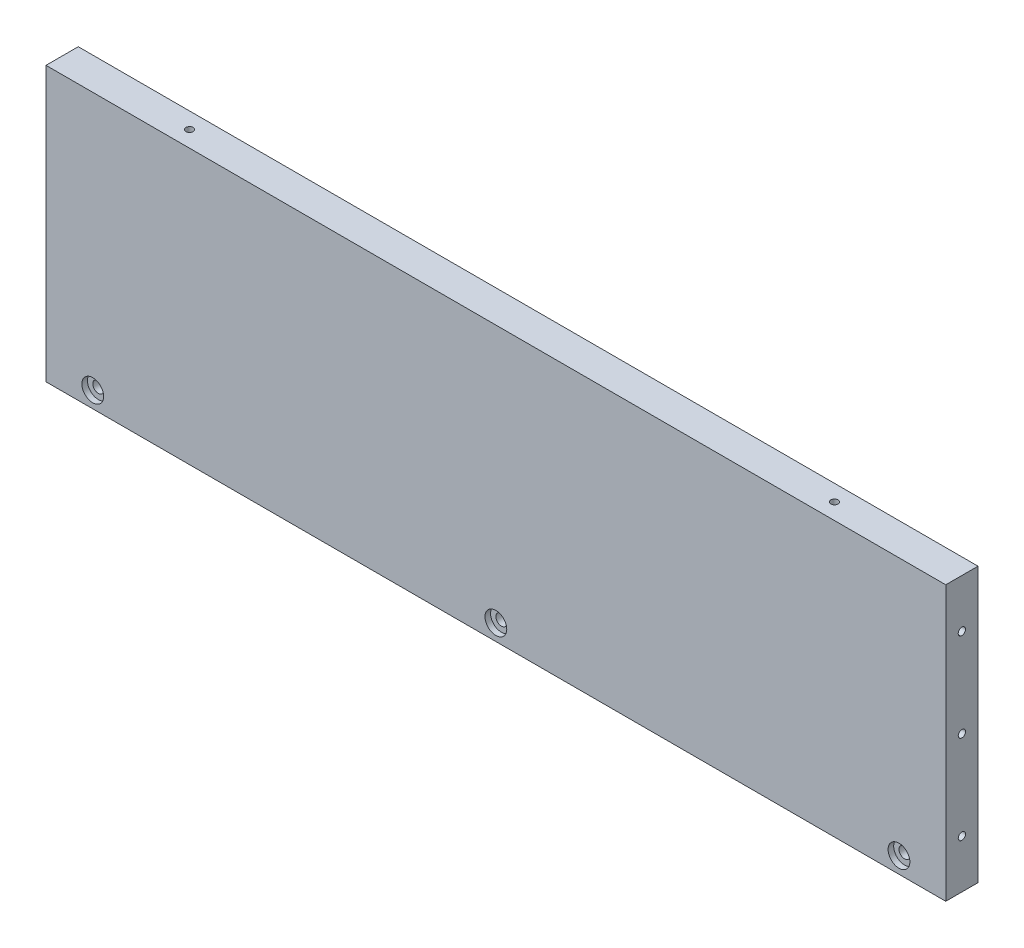
SolidWorks part; units mm, degrees
ref_plane "Front Plane" through (0, 0, 0) normal (0, 0, 1) x (1, 0, 0)
ref_plane "Top Plane" through (0, 0, 0) normal (0, 1, 0) x (1, 0, 0)
ref_plane "Right Plane" through (0, 0, 0) normal (1, 0, 0) x (0, 0, -1)
sketch "Sketch1" plane through (0, 0, 0) normal (0, 0, 1) x (1, 0, 0)
  line L1 (-130.9962, 78.0328) -> (148.0038, 78.0328)
  line L2 (-130.9962, 78.0328) -> (-130.9962, -6.9672)
  line L3 (-130.9962, -6.9672) -> (148.0038, -6.9672)
  line L4 (148.0038, 78.0328) -> (148.0038, -6.9672)
  dimension "D1" = 279
  dimension "D2" = 85
extrude "Boss-Extrude1" add sketch "Sketch1" along normal blind 10
sketch "Sketch2" plane through (0, 0, 10) normal (0, 0, 1) x (1, 0, 0)
  line L0 (-116.4962, -1.9672) -> (133.5038, -1.9672)
  line L1 (-130.9962, -6.9672) -> (148.0038, -6.9672) construction
  point P3 (8.5038, -1.9672)
  point P5 (8.5038, -6.9672)
  dimension "D1" = 5
  dimension "D2" = 250
  dimension "D3" = 0
hole_wizard "CBORE for #4 Binding Head Machine Screw1" positions "Sketch5" profile "Sketch4" counterbore size "#4" standard "ANSI Inch" end condition through all
sketch "Sketch5" plane through (0, 0, 10) normal (0, 0, 1) x (1, 0, 0)
  point P0 (-116.4962, -1.9672)
  point P3 (8.5038, -1.9672)
  point P6 (133.5038, -1.9672)
sketch "Sketch4" plane through (-116.4962, -1.9672, 10) normal (1, 0, 0) x (0, -1, 0)
  line L0 (0, 0) -> (0, 10)
  line L1 (0, 10) -> (1.7272, 10)
  line L3 (1.7272, 10) -> (1.7272, 1.7272)
  line L4 (1.7272, 1.7272) -> (3.3731, 1.7272)
  line L5 (3.3731, 1.7272) -> (3.3731, 0)
  line L7 (3.3731, 0) -> (0, 0)
  line L11 (0, -6.35) -> (0, 107.95) construction
  dimension "Thru Hole Dia." = 3.4544
  dimension "Thru Hole Depth" = 10
  dimension "C'Bore Dia." = 6.7462
  dimension "C'Bore Depth" = 1.7272
sketch "Sketch6" plane through (-130.9962, 0, 0) normal (-1, 0, 0) x (0, 0, 1)
  line L0 (0, 35.5328) -> (10, 35.5328)
  line L1 (0, 78.0328) -> (0, -6.9672) construction
  line L2 (10, 78.0328) -> (10, -6.9672) construction
  line L3 (5, 8.0328) -> (5, 63.0328)
  line L4 (10, 78.0328) -> (0, 78.0328) construction
  point P9 (5, 35.5328)
  dimension "D1" = 15
hole_wizard "#4-40 Tapped Hole1" positions "Sketch7" profile "Sketch8" tap size "#4-40" standard "ANSI Inch"
sketch "Sketch7" plane through (-130.9962, 0, 0) normal (-1, 0, 0) x (0, 0, 1)
  point P0 (5, 63.0328)
  point P3 (5, 35.5328)
  point P6 (5, 8.0328)
sketch "Sketch8" plane through (-130.9962, 63.0328, 5) normal (0, 1, 0) x (0, 0, 1)
  line L0 (0, 0) -> (0, 8.2792)
  line L1 (0, 8.2792) -> (1.1303, 7.6)
  line L2 (1.1303, 7.6) -> (1.1303, 0)
  line L5 (1.1303, 0) -> (0, 0)
  line L10 (0, 8.2792) -> (-1.1303, 7.6) construction
  line L11 (0, -6.35) -> (0, 107.95) construction
  dimension "Tap Drill Dia." = 2.2606
  dimension "Tap Drill Depth" = 7.6
  dimension "Drill Angle" = 118
cosmetic thread "Hole Thread1" parameters "D1"=5.69, "D2"=2.8448
cosmetic thread "Hole Thread2" parameters "D1"=5.69, "D2"=2.8448
cosmetic thread "Hole Thread3" parameters "D1"=5.69, "D2"=2.8448
sketch "Sketch9" plane through (148.0038, 0, 0) normal (1, 0, 0) x (0, 0, -1)
  line L0 (-5, 8.0328) -> (-5, 63.0328)
  point P3 (-5, 35.5328)
hole_wizard "#4-40 Tapped Hole2" positions "Sketch10" profile "Sketch11" tap size "#4-40" standard "ANSI Inch"
sketch "Sketch10" plane through (148.0038, 0, 0) normal (1, 0, 0) x (0, 0, -1)
  line L0 (0, 35.5328) -> (-10, 35.5328) construction
  point P0 (-5, 63.0328)
  point P3 (-5, 35.5328)
  point P7 (-5, 8.0328)
sketch "Sketch11" plane through (148.0038, 63.0328, 5) normal (0, 1, 0) x (0, 0, -1)
  line L0 (0, 0) -> (0, 8.2792)
  line L1 (0, 8.2792) -> (1.1303, 7.6)
  line L2 (1.1303, 7.6) -> (1.1303, 0)
  line L5 (1.1303, 0) -> (0, 0)
  line L10 (0, 8.2792) -> (-1.1303, 7.6) construction
  line L11 (0, -6.35) -> (0, 107.95) construction
  dimension "Tap Drill Dia." = 2.2606
  dimension "Tap Drill Depth" = 7.6
  dimension "Drill Angle" = 118
cosmetic thread "Hole Thread4" parameters "D1"=5.69, "D2"=2.8448
cosmetic thread "Hole Thread5" parameters "D1"=5.69, "D2"=2.8448
cosmetic thread "Hole Thread6" parameters "D1"=5.69, "D2"=2.8448
sketch "Sketch12" plane through (0, 78.0328, 0) normal (0, 1, 0) x (1, 0, 0)
  line L0 (-130.9962, -5) -> (148.0038, -5)
  line L1 (-130.9962, 0) -> (-130.9962, -10) construction
  line L2 (8.5038, -10) -> (8.5038, 0)
  line L3 (148.0038, 0) -> (-130.9962, 0) construction
  point P10 (-91.4962, -5)
  point P11 (108.5038, -5)
  dimension "D1" = 100
hole_wizard "#4-40 Tapped Hole3" positions "Sketch13" profile "Sketch14" tap size "#4-40" standard "ANSI Inch"
sketch "Sketch13" plane through (0, 78.0328, 0) normal (0, 1, 0) x (1, 0, 0)
  point P0 (-91.4962, -5)
  point P3 (108.5038, -5)
sketch "Sketch14" plane through (-91.4962, 78.0328, 5) normal (1, 0, 0) x (0, 0, 1)
  line L0 (0, 0) -> (0, 8.2792)
  line L1 (0, 8.2792) -> (1.1303, 7.6)
  line L2 (1.1303, 7.6) -> (1.1303, 0)
  line L5 (1.1303, 0) -> (0, 0)
  line L10 (0, 8.2792) -> (-1.1303, 7.6) construction
  line L11 (0, -6.35) -> (0, 107.95) construction
  dimension "Tap Drill Dia." = 2.2606
  dimension "Tap Drill Depth" = 7.6
  dimension "Drill Angle" = 118
cosmetic thread "Hole Thread7" parameters "D1"=5.69, "D2"=2.8448
cosmetic thread "Hole Thread8" parameters "D1"=5.69, "D2"=2.8448
